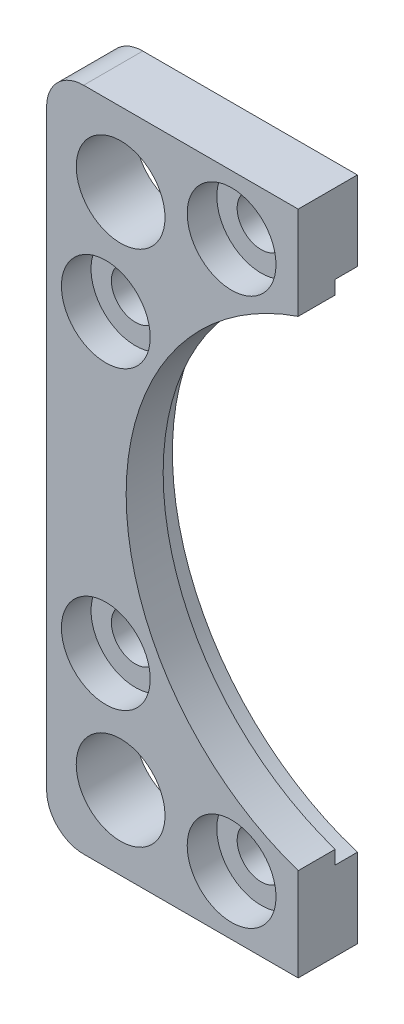
SolidWorks part; units mm, degrees
material "1060 Alloy"
ref_plane "Front Plane" through (0, 0, 0) normal (0, 0, 1) x (1, 0, 0)
ref_plane "Top Plane" through (0, 0, 0) normal (0, 1, 0) x (1, 0, 0)
ref_plane "Right Plane" through (0, 0, 0) normal (1, 0, 0) x (0, 0, -1)
sketch "Sketch1" plane through (0, 0, 0) normal (0, 0, 1) x (1, 0, 0)
  line L0 (-35, 45) -> (-35, 35) construction
  line L1 (-45, -45) -> (45, -45) construction
  line L2 (-45, -45) -> (-45, 45) construction
  line L3 (-45, 45) -> (45, 45) construction
  line L4 (45, -45) -> (45, 45) construction
  line L5 (-45, -45) -> (45, 45) construction
  line L6 (-45, 45) -> (45, -45) construction
  line L7 (-35, 35) -> (-45, 35) construction
  line L8 (-1000, 0) -> (49000, 0) construction
  line L9 (0, -1000) -> (0, 49000) construction
  line L10 (-11, 45) -> (-11, 32.4355)
  line L11 (-11, -45) -> (-11, -32.4355)
  line L12 (-11, 45) -> (-45, 45)
  line L13 (-45, 45) -> (-45, -45)
  line L14 (-45, -45) -> (-11, -45)
  arc A0 (-11, 32.4355) -> (-11, -32.4355) centre (0, 0) ccw
  circle A1 centre (-35, 35) radius 6
  circle A2 centre (-35, -35) radius 6
  circle A3 centre (-37, 20) radius 3.25
  circle A4 centre (-37, -20) radius 3.25
  circle A5 centre (-20, 37) radius 3.25
  circle A6 centre (-20, -37) radius 3.25
  point P0 (0, 0)
  dimension "D2" = 68.5
  dimension "D4" = 12
  dimension "D6" = 6.5
  dimension "D1" = 90
  dimension "D3" = 10
  dimension "D5" = 8
  dimension "D7" = 20
  dimension "D8" = 8
  dimension "D9" = 20
  dimension "D10" = 34
extrude "Boss-Extrude1" add sketch "Sketch1" along normal mid plane 8
sketch "Sketch2" plane through (0, 0, -4) normal (0, 0, -1) x (-1, 0, 0)
  circle A0 centre (0, 0) radius 36
  dimension "D1" = 72
extrude "Cut-Extrude1" cut sketch "Sketch2" against normal blind 3
fillet "Fillet1" radius 5 2 edges at (-45, -45, 0) (-45, 45, 0)
sketch "Sketch3" plane through (0, 0, 4) normal (0, 0, 1) x (1, 0, 0)
  line L0 (-1000, 0) -> (49000, 0) construction
  circle A0 centre (-20, 37) radius 6
  circle A1 centre (-37, 20) radius 6
  circle A2 centre (-37, -20) radius 6
  circle A3 centre (-20, -37) radius 6
  dimension "D1" = 12
extrude "Cut-Extrude2" cut sketch "Sketch3" against normal blind 4
